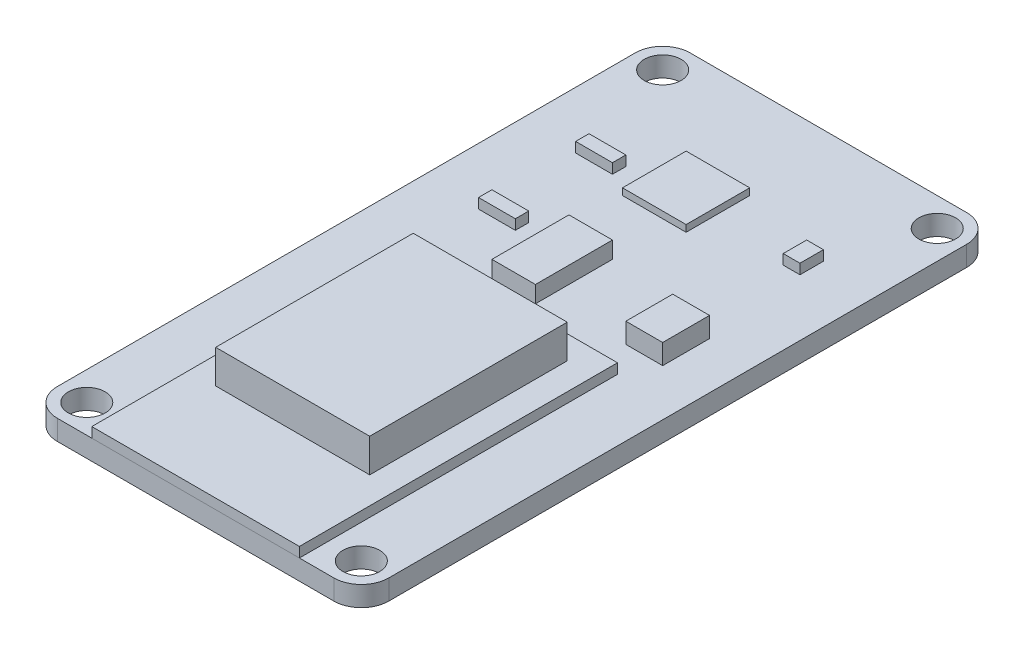
SolidWorks part; units mm, degrees
ref_plane "Front" through (0, 0, 0) normal (0, 0, 1) x (1, 0, 0)
ref_plane "Top" through (0, 0, 0) normal (0, 1, 0) x (1, 0, 0)
ref_plane "Right" through (0, 0, 0) normal (1, 0, 0) x (0, 0, -1)
sketch "Sketch1" plane through (0, 0, 0) normal (0, 1, 0) x (1, 0, 0)
  line L1 (-12.573, 24.003) -> (12.573, 24.003)
  line L2 (-12.573, 24.003) -> (-12.573, -24.003)
  line L3 (-12.573, -24.003) -> (12.573, -24.003)
  line L4 (12.573, 24.003) -> (12.573, -24.003)
  line L5 (-12.573, 24.003) -> (12.573, -24.003) construction
  line L6 (-12.573, -24.003) -> (12.573, 24.003) construction
  point P0 (0, 0)
  dimension "D1" = 48.006
  dimension "D2" = 25.146
extrude "Boss-Extrude1" add sketch "Sketch1" along normal blind 1.524
sketch "Sketch3" plane through (0, 1.524, 0) normal (0, 1, 0) x (1, 0, 0)
  line L0 (0, 0) -> (0, -11.938) construction
  line L1 (-7.874, 0.127) -> (7.874, 0.127)
  line L2 (-7.874, 0.127) -> (-7.874, -24.003)
  line L3 (-7.874, -24.003) -> (7.874, -24.003)
  line L4 (7.874, 0.127) -> (7.874, -24.003)
  line L5 (-7.874, 0.127) -> (7.874, -24.003) construction
  line L6 (-7.874, -24.003) -> (7.874, 0.127) construction
  line L7 (-12.573, -24.003) -> (12.573, -24.003) construction
  point P0 (0, -11.938)
  point P10 (-8.3749, -2.4593)
  dimension "D1" = 24.13
  dimension "D2" = 15.748
extrude "Boss-Extrude3" add sketch "Sketch3" along normal blind 0.762 separate body
sketch "Sketch2" plane through (0, 2.286, 0) normal (0, 1, 0) x (1, 0, 0)
  line L0 (0, -9.144) -> (0, 0) construction
  line L1 (-5.842, -1.651) -> (5.842, -1.651)
  line L2 (-5.842, -1.651) -> (-5.842, -16.637)
  line L3 (-5.842, -16.637) -> (5.842, -16.637)
  line L4 (5.842, -1.651) -> (5.842, -16.637)
  line L5 (-5.842, -1.651) -> (5.842, -16.637) construction
  line L6 (-5.842, -16.637) -> (5.842, -1.651) construction
  line L7 (-12.573, -24.003) -> (12.573, -24.003) construction
  point P0 (0, -9.144)
  dimension "D1" = 7.366
  dimension "D2" = 14.986
  dimension "D3" = 11.684
extrude "Boss-Extrude2" add sketch "Sketch2" along normal blind 2.54 separate body
sketch "Sketch6" plane through (0, 1.524, 0) normal (0, 1, 0) x (1, 0, 0)
  line L0 (12.573, -24.003) -> (12.573, 24.003) construction
  line L1 (-10.414, 21.844) -> (10.414, 21.844) construction
  line L2 (-10.414, 21.844) -> (-10.414, -21.844) construction
  line L3 (-10.414, -21.844) -> (10.414, -21.844) construction
  line L4 (10.414, 21.844) -> (10.414, -21.844) construction
  line L5 (-12.573, -24.003) -> (12.573, -24.003) construction
  line L6 (0, 0) -> (0, -21.844) construction
  line L7 (0, 0) -> (10.414, 0) construction
  circle A0 centre (10.414, 21.844) radius 1.397
  circle A1 centre (-10.414, 21.844) radius 1.397
  circle A2 centre (-10.414, -21.844) radius 1.397
  circle A3 centre (10.414, -21.844) radius 1.397
  dimension "D1" = 2.794
  dimension "D2" = 0.762
  dimension "D3" = 0.762
extrude "Cut-Extrude1" cut sketch "Sketch6" against normal through all
fillet "Fillet1" radius 2.0828 4 edges at (-12.573, 0.762, -24.003) (12.573, 0.762, -24.003) (12.573, 0.762, 24.003) (-12.573, 0.762, 24.003)
sketch "Sketch7" plane through (0, 1.524, 0) normal (0, 1, 0) x (1, 0, 0)
  line L0 (-12.573, 21.9202) -> (-12.573, -21.9202) construction
  line L1 (-3.175, 7.493) -> (0.127, 7.493)
  line L2 (-3.175, 7.493) -> (-3.175, 1.651)
  line L3 (-3.175, 1.651) -> (0.127, 1.651)
  line L4 (0.127, 7.493) -> (0.127, 1.651)
  line L7 (-7.874, -24.003) -> (7.874, -24.003) construction
  dimension "D1" = 9.398
  dimension "D2" = 3.302
  dimension "D3" = 5.842
  dimension "D4" = 31.496
extrude "Boss-Extrude4" add sketch "Sketch7" along normal blind 1.27
sketch "Sketch8" plane through (0, 1.524, 0) normal (0, 1, 0) x (1, 0, 0)
  line L0 (-12.573, 21.9202) -> (-12.573, -21.9202) construction
  line L1 (-3.683, 16.891) -> (1.143, 16.891)
  line L2 (-3.683, 16.891) -> (-3.683, 12.065)
  line L3 (-3.683, 12.065) -> (1.143, 12.065)
  line L4 (1.143, 16.891) -> (1.143, 12.065)
  line L6 (10.4902, 24.003) -> (-10.4902, 24.003) construction
  line L7 (0.127, 7.493) -> (-3.175, 7.493) construction
  dimension "D1" = 4.826
  dimension "D2" = 8.89
  dimension "D3" = 11.938
  dimension "D4" = 4.572
extrude "Boss-Extrude5" add sketch "Sketch8" along normal blind 0.508
sketch "Sketch9" plane through (0, 1.524, 0) normal (0, 1, 0) x (1, 0, 0)
  line L0 (12.573, -21.9202) -> (12.573, 21.9202) construction
  line L1 (6.223, 5.969) -> (9.017, 5.969)
  line L2 (6.223, 5.969) -> (6.223, 2.413)
  line L3 (6.223, 2.413) -> (9.017, 2.413)
  line L4 (9.017, 5.969) -> (9.017, 2.413)
  line L5 (7.874, 0.127) -> (-7.874, 0.127) construction
  dimension "D1" = 2.794
  dimension "D2" = 3.556
  dimension "D3" = 3.556
  dimension "D4" = 2.286
extrude "Boss-Extrude6" add sketch "Sketch9" along normal blind 1.524
sketch "Sketch10" plane through (0, 1.524, 0) normal (0, 1, 0) x (1, 0, 0)
  line L0 (-3.175, 7.493) -> (-3.175, 1.651) construction
  line L1 (-8.255, 6.731) -> (-5.461, 6.731)
  line L2 (-8.255, 6.731) -> (-8.255, 5.715)
  line L3 (-8.255, 5.715) -> (-5.461, 5.715)
  line L4 (-5.461, 6.731) -> (-5.461, 5.715)
  line L5 (-8.255, 14.097) -> (-5.461, 14.097)
  line L6 (-8.255, 14.097) -> (-8.255, 13.081)
  line L7 (-8.255, 13.081) -> (-5.461, 13.081)
  line L8 (-5.461, 14.097) -> (-5.461, 13.081)
  line L9 (6.985, 15.367) -> (8.255, 15.367)
  line L10 (6.985, 15.367) -> (6.985, 13.589)
  line L11 (6.985, 13.589) -> (8.255, 13.589)
  line L12 (8.255, 15.367) -> (8.255, 13.589)
  line L13 (10.4902, 24.003) -> (-10.4902, 24.003) construction
  line L16 (12.573, -21.9202) -> (12.573, 21.9202) construction
  dimension "D1" = 1.27
  dimension "D2" = 1.778
  dimension "D3" = 2.794
  dimension "D4" = 1.016
  dimension "D5" = 2.286
  dimension "D6" = 8.382
  dimension "D7" = 18.288
  dimension "D8" = 5.588
  dimension "D9" = 10.414
extrude "Boss-Extrude7" add sketch "Sketch10" along normal blind 0.762
